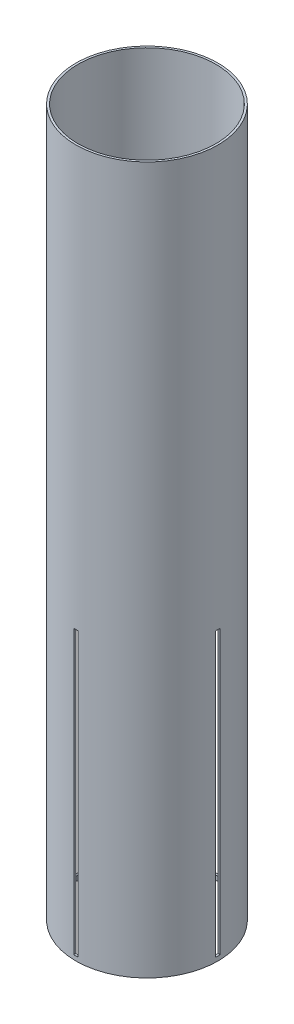
SolidWorks part; units mm, degrees
ref_plane "Front Plane" through (0, 0, 0) normal (0, 0, 1) x (1, 0, 0)
ref_plane "Top Plane" through (0, 0, 0) normal (0, 1, 0) x (1, 0, 0)
ref_plane "Right Plane" through (0, 0, 0) normal (1, 0, 0) x (0, 0, -1)
sketch "Sketch1" plane through (0, 0, 0) normal (0, 1, 0) x (1, 0, 0)
  circle A0 centre (0, 0) radius 49.53
  circle A1 centre (0, 0) radius 51.054
  dimension "D1" = 99.06
  dimension "D2" = 102.108
extrude "Boss-Extrude1" add sketch "Sketch1" along normal blind 508
sketch "Sketch2" plane through (0, 0, 0) normal (0, 0, 1) x (1, 0, 0)
  line L0 (-51.054, 0) -> (51.054, 0) construction
  line L1 (-1.5875, 206.375) -> (1.5875, 206.375)
  line L2 (-1.5875, 206.375) -> (-1.5875, 3.175)
  line L3 (-1.5875, 3.175) -> (1.5875, 3.175)
  line L4 (1.5875, 206.375) -> (1.5875, 3.175)
  point P4 (17.9423, 21.2547)
  point P5 (0, 3.175)
  dimension "D1" = 3.175
  dimension "D2" = 203.2
  dimension "D3" = 3.175
extrude "Cut-Extrude1" cut sketch "Sketch2" against normal through all
pattern_circular "CirPattern1" count 4 over 360 about axis through (0, 0, 0) along (0, 1, 0) of "Cut-Extrude1"
